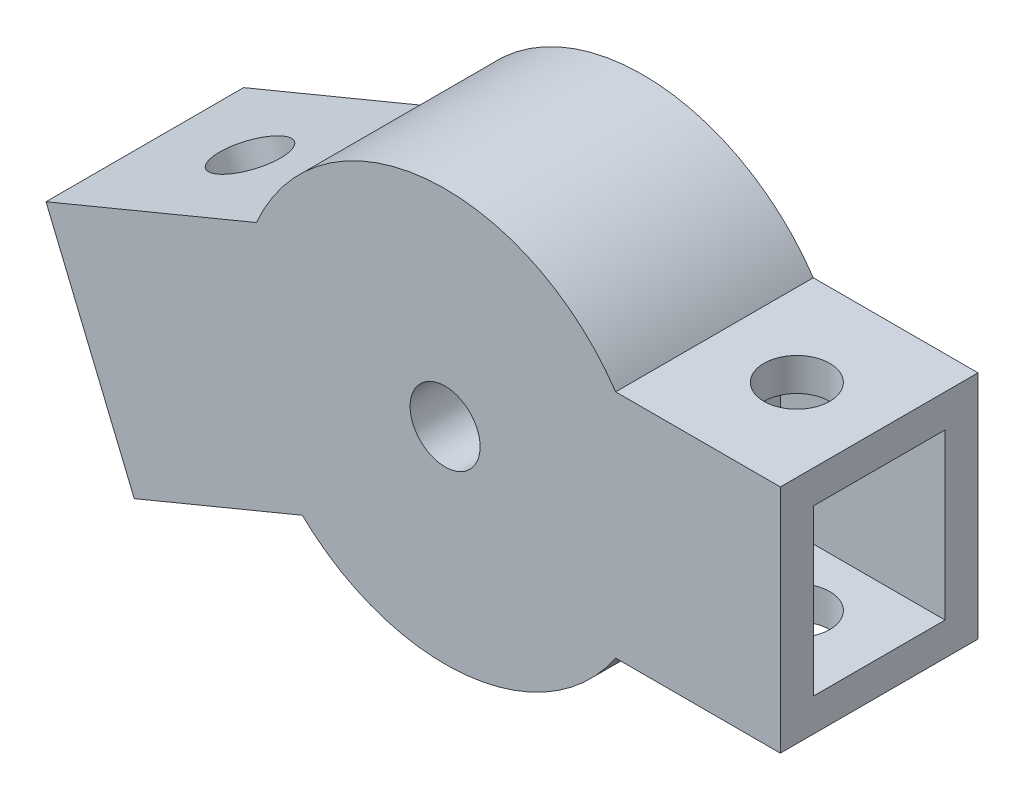
SolidWorks part; units mm, degrees
ref_plane "Front Plane" through (0, 0, 0) normal (0, 0, 1) x (1, 0, 0)
ref_plane "Top Plane" through (0, 0, 0) normal (0, 1, 0) x (1, 0, 0)
ref_plane "Right Plane" through (0, 0, 0) normal (1, 0, 0) x (0, 0, -1)
sketch "Sketch1" plane through (0, 0, 0) normal (0, 0, 1) x (1, 0, 0)
  line L0 (0, 0) -> (-12.5, 0) construction
  line L1 (0, 0) -> (-11.5485, -4.7835) construction
  line L2 (-24.2314, -0.2955) -> (-11.4585, 4.9953)
  line L3 (0, 0) -> (0, 10) construction
  line L4 (-18.8739, -13.2298) -> (-8.671, -9.0036)
  line L5 (-20.7873, -8.6104) -> (-18.8739, -13.2298)
  line L6 (-20.7873, -8.6104) -> (-24.2314, -0.2955)
  line L8 (0, 0) -> (12.5, 0) construction
  line L9 (12.5, 0) -> (12.5, 7) construction
  line L12 (-20.7873, -8.6104) -> (-11.5485, -4.7835) construction
  line L15 (10.3562, 7) -> (20.3562, 7)
  line L17 (20.3562, 7) -> (20.3562, -7)
  line L18 (20.3562, -7) -> (10.3562, -7)
  circle A3 centre (0, 0) radius 12.5
  circle A4 centre (0, 0) radius 10
  dimension "D1" = 25
  dimension "D3" = 22.5
  dimension "D2" = 20
  dimension "D4" = 10
  dimension "D5" = 9
  dimension "D6" = 5
  dimension "D7" = 7
  dimension "D8" = 14
extrude "Boss-Extrude2" add sketch "Sketch1" along normal blind 12 contours A3
sketch "Sketch5" plane through (0, 0, 12) normal (0, 0, 1) x (1, 0, 0)
  line L0 (0, 0) -> (0, 10) construction
  line L1 (0, 0) -> (10, 0) construction
  circle A7 centre (0, 0) radius 2.125
  point P17 (0, 0)
  dimension "D1" = 4.25
extrude "Cut-Extrude3" cut sketch "Sketch5" against normal up to next
sketch "Sketch6" plane through (0, 0, 0) normal (0, 0, 1) x (1, 0, 0)
  line L0 (10.3562, 7) -> (20.3562, 7) construction
  line L1 (20.3562, 7) -> (20.3562, -7) construction
  line L2 (20.3562, -7) -> (10.3562, -7) construction
  line L3 (-24.2314, -0.2955) -> (-11.4585, 4.9953) construction
  line L4 (-20.7873, -8.6104) -> (-24.2314, -0.2955) construction
  line L5 (-20.7873, -8.6104) -> (-18.8739, -13.2298) construction
  line L6 (-18.8739, -13.2298) -> (-8.671, -9.0036) construction
  line L7 (10.3562, 7) -> (20.3562, 7)
  line L8 (20.3562, 7) -> (20.3562, -7)
  line L9 (20.3562, -7) -> (10.3562, -7)
  line L10 (-24.2314, -0.2955) -> (-11.4585, 4.9953)
  line L11 (-20.7873, -8.6104) -> (-24.2314, -0.2955)
  line L12 (-20.7873, -8.6104) -> (-18.8739, -13.2298)
  line L13 (-18.8739, -13.2298) -> (-8.671, -9.0036)
  arc A0 (10.3562, -7) -> (10.3562, 7) centre (0, 0) ccw
  circle A3 centre (0, 0) radius 12.5
  arc A4 (-11.4585, 4.9953) -> (-8.671, -9.0036) centre (0, 0) ccw
  dimension "D2" = 0
extrude "Boss-Extrude3" add sketch "Sketch6" along normal blind 12
sketch "Sketch8" plane through (0, 0, 0) normal (0, 0, -1) x (-1, 0, 0)
  circle A0 centre (0, 0) radius 6
sketch "Sketch9" plane through (20.3562, 0, 0) normal (1, 0, 0) x (0, 0, -1)
  line L0 (-12, -7) -> (-12, 7) construction
  line L1 (-10, 5) -> (-2, 5)
  line L2 (-10, 5) -> (-10, -5)
  line L3 (-10, -5) -> (-2, -5)
  line L4 (-2, 5) -> (-2, -5)
  line L5 (0, -7) -> (0, 7) construction
  line L6 (-12, 7) -> (0, 7) construction
  line L7 (-12, -7) -> (0, -7) construction
  dimension "D1" = 2
  dimension "D2" = 2
  dimension "D3" = 2
  dimension "D4" = 2
extrude "Cut-Extrude4" cut sketch "Sketch9" against normal blind 10
sketch "Sketch10" plane through (-20.7873, -8.6104, 0) normal (-0.9239, -0.3827, 0) x (0, 0, 1)
  line L0 (12, 9) -> (0, 9) construction
  line L1 (2, 7) -> (10, 7)
  line L2 (2, 7) -> (2, -3)
  line L3 (2, -3) -> (10, -3)
  line L4 (10, 7) -> (10, -3)
  line L5 (12, -5) -> (0, -5) construction
  line L6 (12, 9) -> (12, -5) construction
  line L7 (0, 6) -> (0, -6) construction
  dimension "D1" = 2
  dimension "D2" = 2
  dimension "D3" = 2
  dimension "D4" = 2
extrude "Cut-Extrude5" cut sketch "Sketch10" against normal blind 10
sketch "Sketch11" plane through (0, 7, 0) normal (0, 1, 0) x (1, 0, 0)
  line L0 (15.3562, 0) -> (15.3562, -12) construction
  line L1 (20.3562, 0) -> (10.3562, 0) construction
  line L2 (20.3562, -12) -> (10.3562, -12) construction
  line L3 (10.3562, -6) -> (20.3562, -6) construction
  line L4 (10.3562, -12) -> (10.3562, 0) construction
  line L5 (20.3562, -12) -> (20.3562, 0) construction
  circle A0 centre (15.3562, -6) radius 2
extrude "Cut-Extrude6" cut sketch "Sketch11" against normal through all
sketch "Sketch12" plane through (-3.4442, 8.3149, 0) normal (-0.3827, 0.9239, 0) x (0.9239, 0.3827, 0)
  line L0 (-15.5873, 0) -> (-15.5873, -12) construction
  line L1 (-8.6747, 0) -> (-22.5, 0) construction
  line L2 (-8.6747, -12) -> (-22.5, -12) construction
  line L3 (-22.5, -6) -> (-8.6747, -6) construction
  line L4 (-22.5, -12) -> (-22.5, 0) construction
  line L5 (-8.6747, -12) -> (-8.6747, 0) construction
  circle A0 centre (-15.5873, -6) radius 2
extrude "Cut-Extrude7" cut sketch "Sketch12" against normal through all
